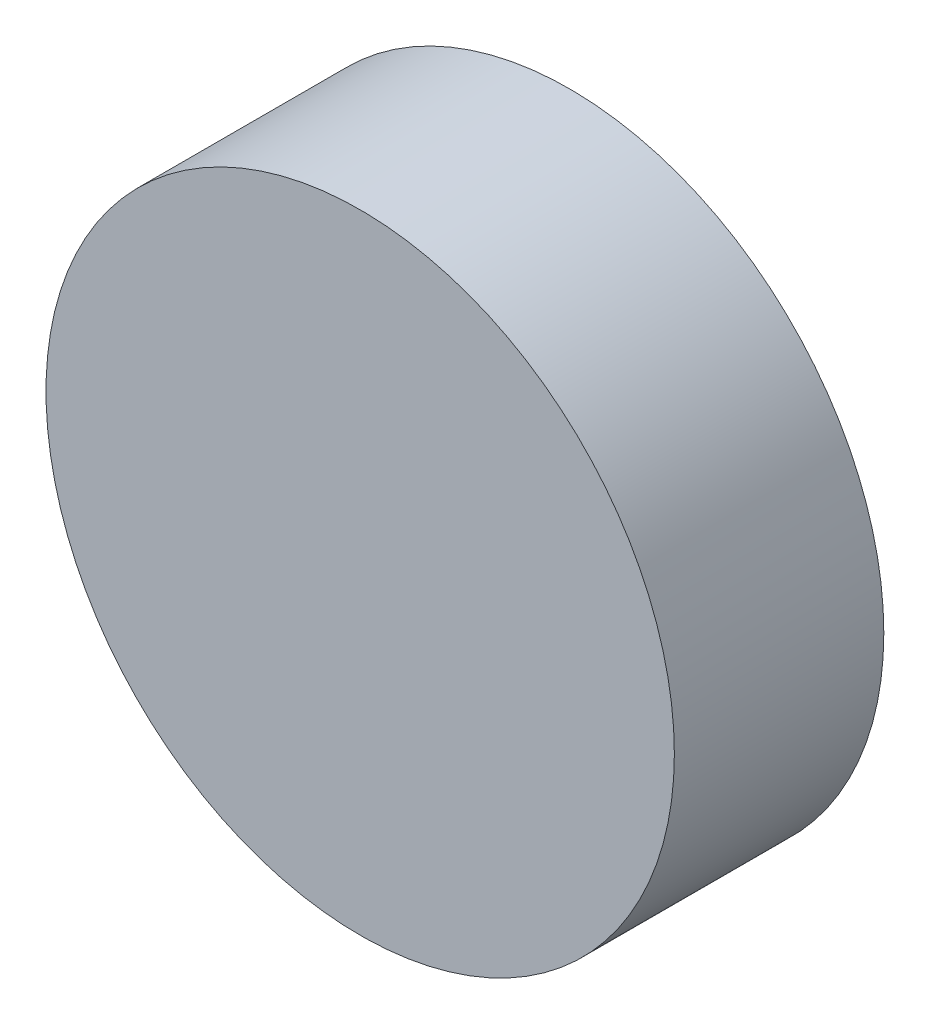
SolidWorks part; units mm, degrees
ref_plane "前视基准面" through (0, 0, 0) normal (0, 0, 1) x (1, 0, 0)
ref_plane "上视基准面" through (0, 0, 0) normal (0, 1, 0) x (1, 0, 0)
ref_plane "右视基准面" through (0, 0, 0) normal (1, 0, 0) x (0, 0, -1)
sketch "草图1" plane through (0, 0, 0) normal (0, 0, 1) x (1, 0, 0)
  circle A0 centre (0, 0) radius 15
  dimension "D1" = 30
extrude "凸台-拉伸1" add sketch "草图1" along normal blind 10
